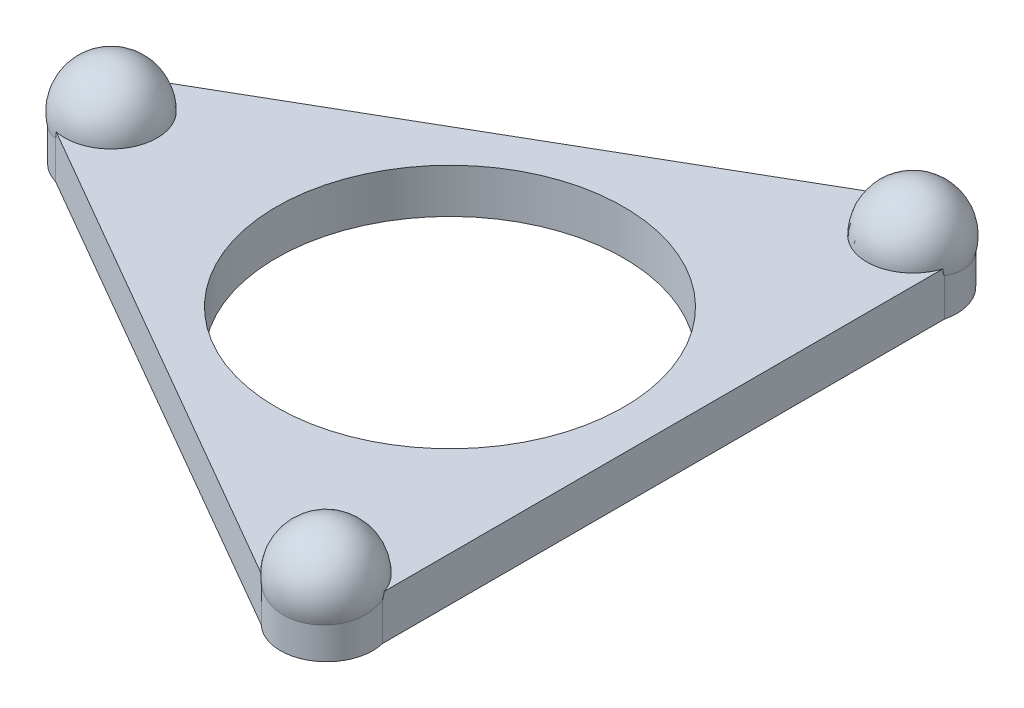
SolidWorks part; units mm, degrees
material "Stainless Steel (ferritic)"
ref_plane "Front Plane" through (0, 0, 0) normal (0, 0, 1) x (1, 0, 0)
ref_plane "Top Plane" through (0, 0, 0) normal (0, 1, 0) x (1, 0, 0)
ref_plane "Right Plane" through (0, 0, 0) normal (1, 0, 0) x (0, 0, -1)
sketch "Sketch1" plane through (0, 0, 0) normal (0, 1, 0) x (1, 0, 0)
  line L0 (-11.59, 1.5875) -> (-0.6409, 1.5875) construction
  line L1 (-11.59, 0) -> (0, 0) construction
  line L2 (7.3371, 9.6602) -> (4.6974, 11.1842) construction
  line L3 (-12.0345, -1.524) -> (-0.9403, -1.524) construction
  line L4 (7.1698, 9.2435) -> (1.6953, -0.2387) construction
  line L5 (0, 0) -> (0, -6.477) construction
  line L6 (4.6974, 11.1842) -> (-0.8496, 1.5764) construction
  line L7 (4.6974, -11.1842) -> (7.3371, -9.6602) construction
  line L8 (4.4202, -10.831) -> (-1.0544, -1.3488) construction
  line L9 (7.3371, -9.6602) -> (1.79, -0.0524) construction
  line L10 (-12.0345, 1.524) -> (-12.0345, -1.524) construction
  line L11 (5.795, 10.0372) -> (0, 0) construction
  line L12 (0, 0) -> (5.795, -10.0372) construction
  line L13 (-12.0345, 1.524) -> (4.6974, 11.1842)
  line L14 (7.3371, 9.6602) -> (7.3371, -9.6602)
  line L15 (4.6974, -11.1842) -> (-12.0345, -1.524)
  circle A0 centre (0, 0) radius 5.969
  circle A1 centre (0, 0) radius 6.477
  circle A2 centre (-11.59, 0) radius 1.5875
  circle A7 centre (5.795, 10.0372) radius 1.5875
  circle A8 centre (5.795, -10.0372) radius 1.5875
  point P26 (0, 0)
  point P29 (0, 0)
  point P33 (0, 0)
  dimension "D4" = 11.938
  dimension "D5" = 12.954
  dimension "D1" = 3.175
  dimension "D2" = 3
  dimension "D3" = 6.477
extrude "Boss-Extrude1" add sketch "Sketch1" along normal blind 1.524
sketch "Sketch2" plane through (0, 1.524, 0) normal (0, 1, 0) x (1, 0, 0)
  line L0 (-11.6522, 1.5875) -> (-11.6522, -1.5875) construction
  line L1 (-11.6522, -1.5875) -> (-11.6522, 1.5875)
  line L4 (0, 0) -> (-13.208, 0) construction
  arc A0 (-11.6522, -1.5875) -> (-11.6522, 1.5875) centre (-11.6522, 0) ccw
  point P7 (-11.6522, 0)
  dimension "D1" = 11.6522
  dimension "D2" = 3.175
sketch "Sketch3" plane through (0, 0, 0) normal (1, 0, 0) x (0, 0, -1)
  line L0 (0, 0) -> (0, 5.5164) construction
sketch "Sketch4" plane through (0, 0, 0) normal (0, 0, 1) x (1, 0, 0)
  line L0 (-11.6522, 1.524) -> (-11.6522, 4.5886) construction
revolve "Revolve1" add sketch "Sketch2" angle 360 about L1
pattern_circular "CirPattern2" count 3 over 360 about axis through (0, 0, 0) along (0, 1, 0) of "Revolve1"
